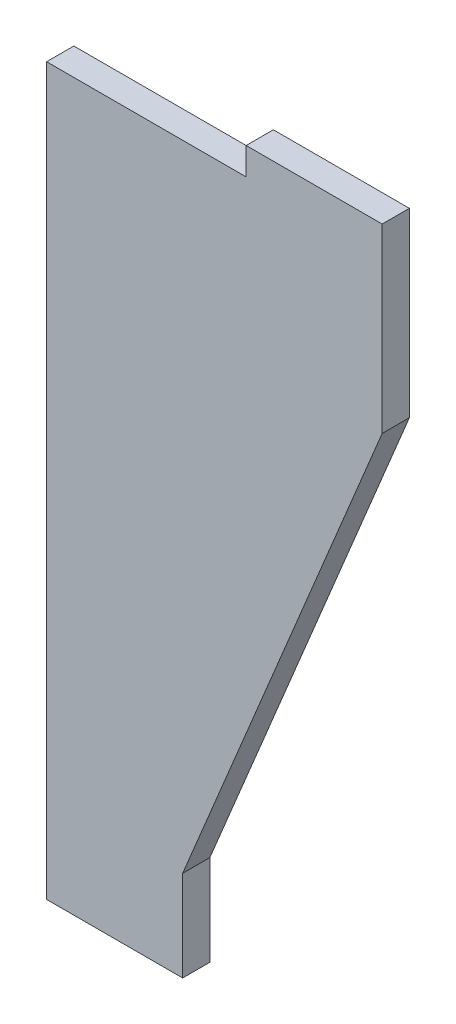
SolidWorks part; units mm, degrees
ref_plane "前视基准面" through (0, 0, 0) normal (0, 0, 1) x (1, 0, 0)
ref_plane "上视基准面" through (0, 0, 0) normal (0, 1, 0) x (1, 0, 0)
ref_plane "右视基准面" through (0, 0, 0) normal (1, 0, 0) x (0, 0, -1)
sketch "草图1" plane through (0, 0, 0) normal (0, 0, 1) x (1, 0, 0)
  line L0 (0, -80) -> (15, -80)
  line L2 (15, -80) -> (15, -70)
  line L3 (15, -70) -> (37, -17)
  line L7 (22, 0) -> (0, 0)
  line L8 (0, 0) -> (0, -80)
  line L9 (37, -17) -> (37, 3)
  line L10 (37, 3) -> (22, 3)
  line L11 (22, 3) -> (22, 0)
  point P3 (41.0537, 1.8974)
  point P7 (13.3833, -96.75)
  point P8 (0, 0)
  point P10 (37, -7.273)
  dimension "D1" = 15
  dimension "D2" = 37
  dimension "D3" = 10
  dimension "D4" = 15
  dimension "D5" = 3
  dimension "D6" = 80
  dimension "D7" = 20
extrude "凸台-拉伸1" add sketch "草图1" against normal blind 3
